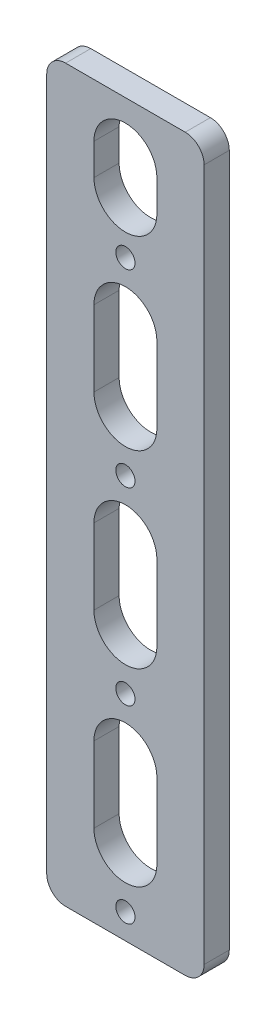
SolidWorks part; units mm, degrees
material "Thornel Mat VMA"
ref_plane "前视基准面" through (0, 0, 0) normal (0, 0, 1) x (1, 0, 0)
ref_plane "上视基准面" through (0, 0, 0) normal (0, 1, 0) x (1, 0, 0)
ref_plane "右视基准面" through (0, 0, 0) normal (1, 0, 0) x (0, 0, -1)
other "Configuration Table"
sketch "草图1" plane through (0, 0, 0) normal (0, 0, 1) x (1, 0, 0)
  line L1 (-12.5, -58) -> (12.5, -58)
  line L2 (-12.5, -58) -> (-12.5, 58)
  line L3 (-12.5, 58) -> (12.5, 58)
  line L4 (12.5, -58) -> (12.5, 58)
  line L5 (-12.5, -58) -> (12.5, 58) construction
  line L6 (-12.5, 58) -> (12.5, -58) construction
  point P0 (0, 0)
  dimension "D1" = 25
  dimension "D2" = 116
extrude "凸台-拉伸1" add sketch "草图1" along normal blind 4
sketch "草图2" plane through (0, 0, 0) normal (0, 0, -1) x (-1, 0, 0)
  circle A0 centre (0, -54) radius 1.525 construction
  circle A1 centre (0, -24) radius 1.525 construction
  circle A2 centre (0, 6) radius 1.525 construction
  circle A3 centre (0, 36) radius 1.525 construction
  circle A4 centre (0, -54) radius 1.525
  circle A5 centre (0, -24) radius 1.525
  circle A6 centre (0, 6) radius 1.525
  circle A7 centre (0, 36) radius 1.525
extrude "切除-拉伸1" cut sketch "草图2" against normal through all both
fillet "圆角1" radius 3 4 edges at (12.5, -58, 2) (-12.5, -58, 2) (12.5, 58, 2) (-12.5, 58, 2)
sketch "草图4" plane through (0, 0, 4) normal (0, 0, 1) x (1, 0, 0)
  line L0 (0, 15) -> (0, 27) construction
  line L1 (-5, 15) -> (-5, 27)
  line L2 (5, 15) -> (5, 27)
  line L3 (0, -45) -> (0, -33) construction
  line L4 (-5, -45) -> (-5, -33)
  line L5 (5, -45) -> (5, -33)
  line L6 (0, -15) -> (0, -3) construction
  line L7 (-5, -15) -> (-5, -3)
  line L8 (5, -15) -> (5, -3)
  line L9 (0, 6) -> (0, -24) construction
  line L10 (0, -24) -> (0, -54) construction
  line L11 (0, 36) -> (0, 6) construction
  line L12 (0, 44.5) -> (0, 49.5) construction
  line L13 (-5, 44.5) -> (-5, 49.5)
  line L14 (5, 44.5) -> (5, 49.5)
  arc A0 (-5, 15) -> (5, 15) centre (0, 15) ccw
  arc A1 (5, 27) -> (-5, 27) centre (0, 27) ccw
  arc A2 (-5, -45) -> (5, -45) centre (0, -45) ccw
  arc A3 (5, -33) -> (-5, -33) centre (0, -33) ccw
  arc A4 (-5, -15) -> (5, -15) centre (0, -15) ccw
  arc A5 (5, -3) -> (-5, -3) centre (0, -3) ccw
  arc A6 (-5, 44.5) -> (5, 44.5) centre (0, 44.5) ccw
  arc A7 (5, 49.5) -> (-5, 49.5) centre (0, 49.5) ccw
  point P3 (0, 21)
  point P8 (0, -39)
  point P15 (0, -9)
  point P31 (0, 47)
  dimension "D2" = 5
  dimension "D3" = 5
  dimension "D1" = 12
  dimension "D4" = 5
  dimension "D5" = 11
extrude "切除-拉伸2" cut sketch "草图4" against normal through all both
